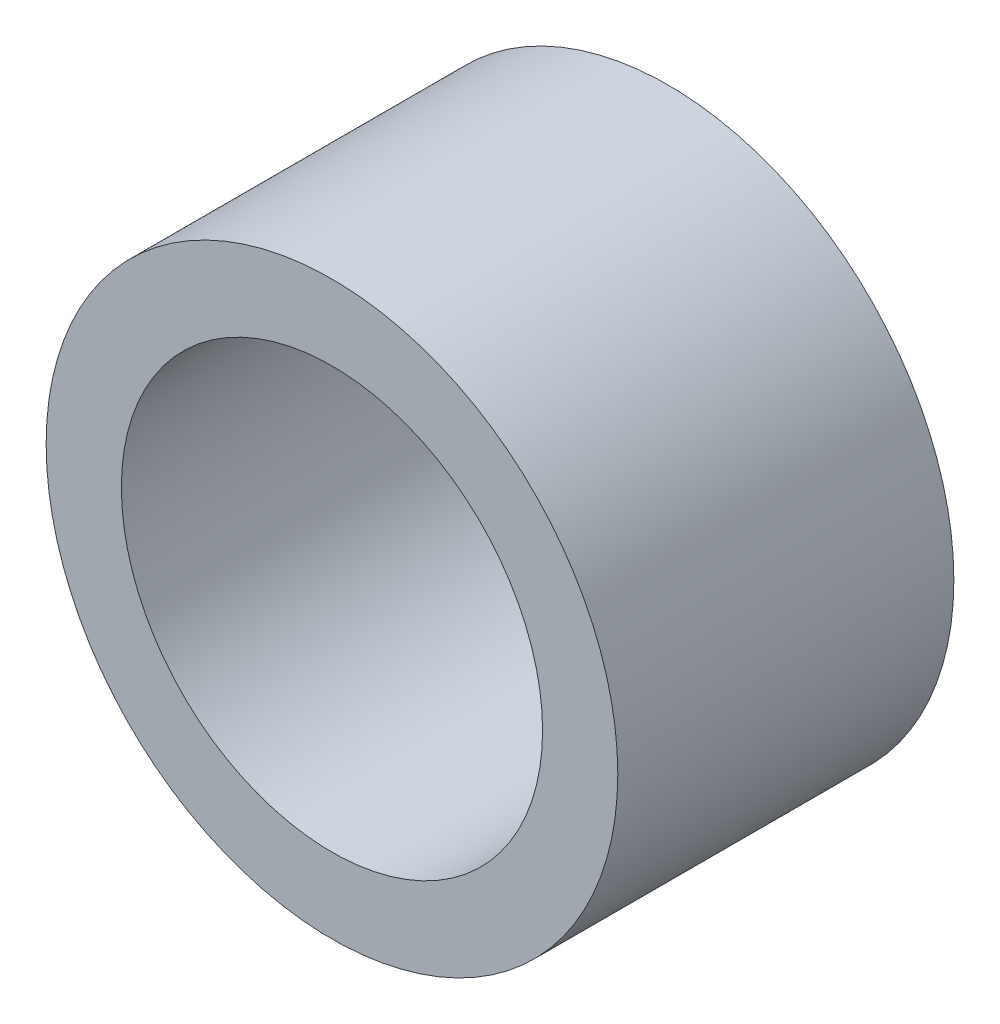
SolidWorks part; units mm, degrees
ref_plane "Front Plane" through (0, 0, 0) normal (0, 0, 1) x (1, 0, 0)
ref_plane "Top Plane" through (0, 0, 0) normal (0, 1, 0) x (1, 0, 0)
ref_plane "Right Plane" through (0, 0, 0) normal (1, 0, 0) x (0, 0, -1)
sketch "Sketch1" plane through (0, 0, 0) normal (0, 0, 1) x (1, 0, 0)
  circle A0 centre (0, 0) radius 4.826
  circle A1 centre (0, 0) radius 3.556
  dimension "D1" = 7.112
  dimension "D2" = 1.27
extrude "Boss-Extrude1" add sketch "Sketch1" along normal blind 5.6744
